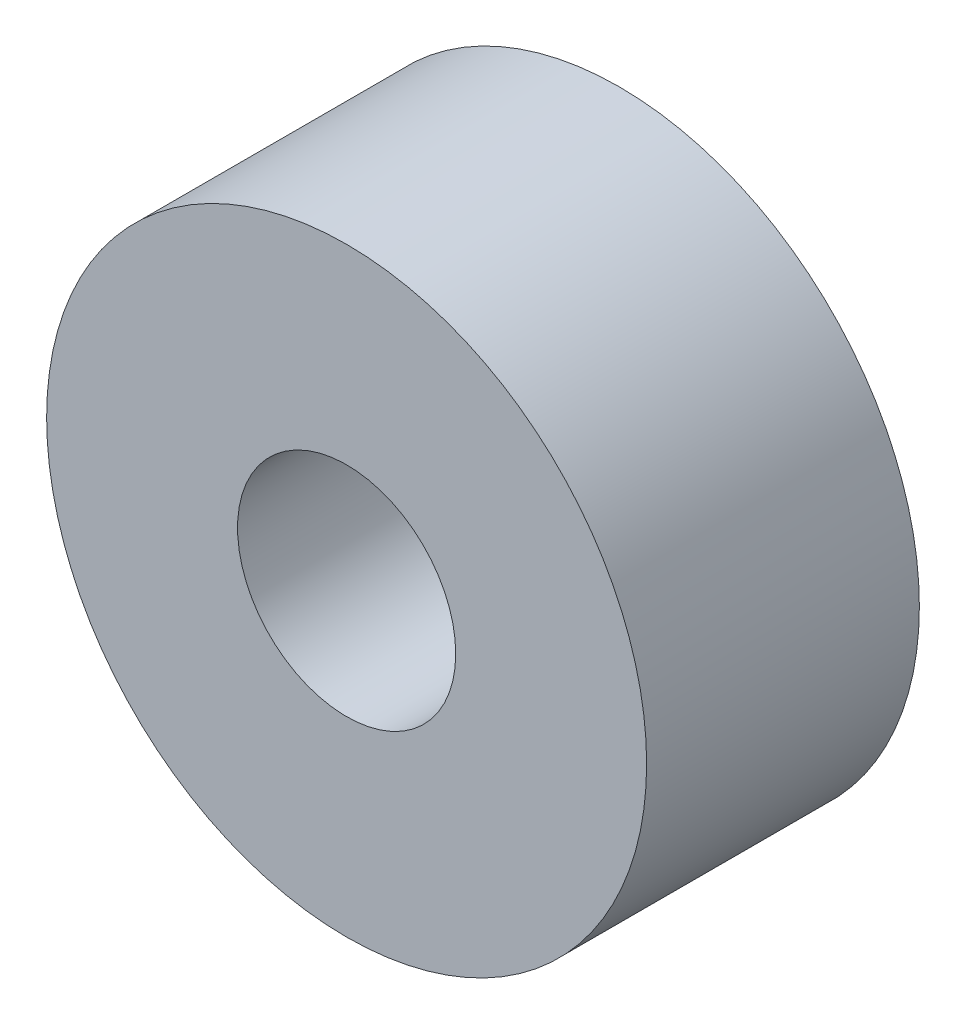
SolidWorks part; units mm, degrees
ref_plane "Ön Düzlem" through (0, 0, 0) normal (0, 0, 1) x (1, 0, 0)
ref_plane "Üst Düzlem" through (0, 0, 0) normal (0, 1, 0) x (1, 0, 0)
ref_plane "Sağ Düzlem" through (0, 0, 0) normal (1, 0, 0) x (0, 0, -1)
sketch "Çizim1" plane through (0, 0, 0) normal (0, 0, 1) x (1, 0, 0)
  circle A0 centre (0, 0) radius 11
  circle A1 centre (0, 0) radius 4
  dimension "D1" = 22
  dimension "D2" = 8
extrude "Yükseklik-Ekstrüzyon1" add sketch "Çizim1" along normal blind 10
